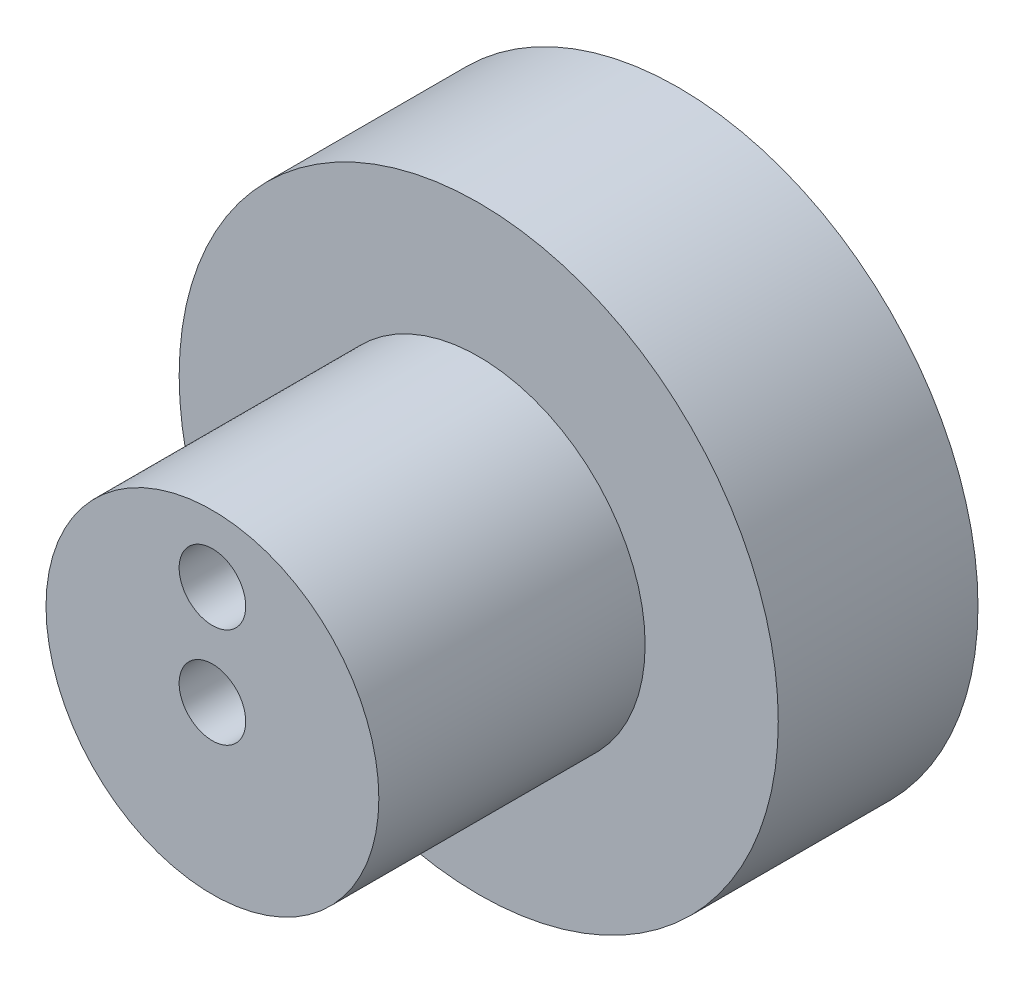
SolidWorks part; units mm, degrees
ref_plane "Plan de face" through (0, 0, 0) normal (0, 0, 1) x (1, 0, 0)
ref_plane "Plan de dessus" through (0, 0, 0) normal (0, 1, 0) x (1, 0, 0)
ref_plane "Plan de droite" through (0, 0, 0) normal (1, 0, 0) x (0, 0, -1)
sketch "Esquisse1" plane through (0, 0, 0) normal (0, 0, 1) x (1, 0, 0)
  circle A0 centre (0, 0) radius 45
  dimension "D1" = 90
extrude "Boss.-Extru.1" add sketch "Esquisse1" along normal blind 30
sketch "Esquisse2" plane through (0, 0, 30) normal (0, 0, 1) x (1, 0, 0)
  circle A0 centre (0, 0) radius 25
  dimension "D1" = 50
extrude "Boss.-Extru.2" add sketch "Esquisse2" along normal blind 40
sketch "Esquisse3" plane through (0, 0, 70) normal (0, 0, 1) x (1, 0, 0)
  circle A0 centre (0, 0) radius 5
  dimension "D1" = 10
extrude "Enlèv. mat.-Extru.1" cut sketch "Esquisse3" against normal through all
sketch "Esquisse6" plane through (0, 0, 70) normal (0, 0, 1) x (1, 0, 0)
  line L0 (0, 0) -> (0, 33.6805) construction
  circle A0 centre (0, 15) radius 5
  dimension "D1" = 10
  dimension "D2" = 15
extrude "Enlèv. mat.-Extru.3" cut sketch "Esquisse6" against normal blind 10
sketch "Esquisse7" plane through (0, 0, 0) normal (0, 0, -1) x (-1, 0, 0)
  circle A0 centre (0, 15) radius 5
extrude "Enlèv. mat.-Extru.4" cut sketch "Esquisse7" against normal blind 10
